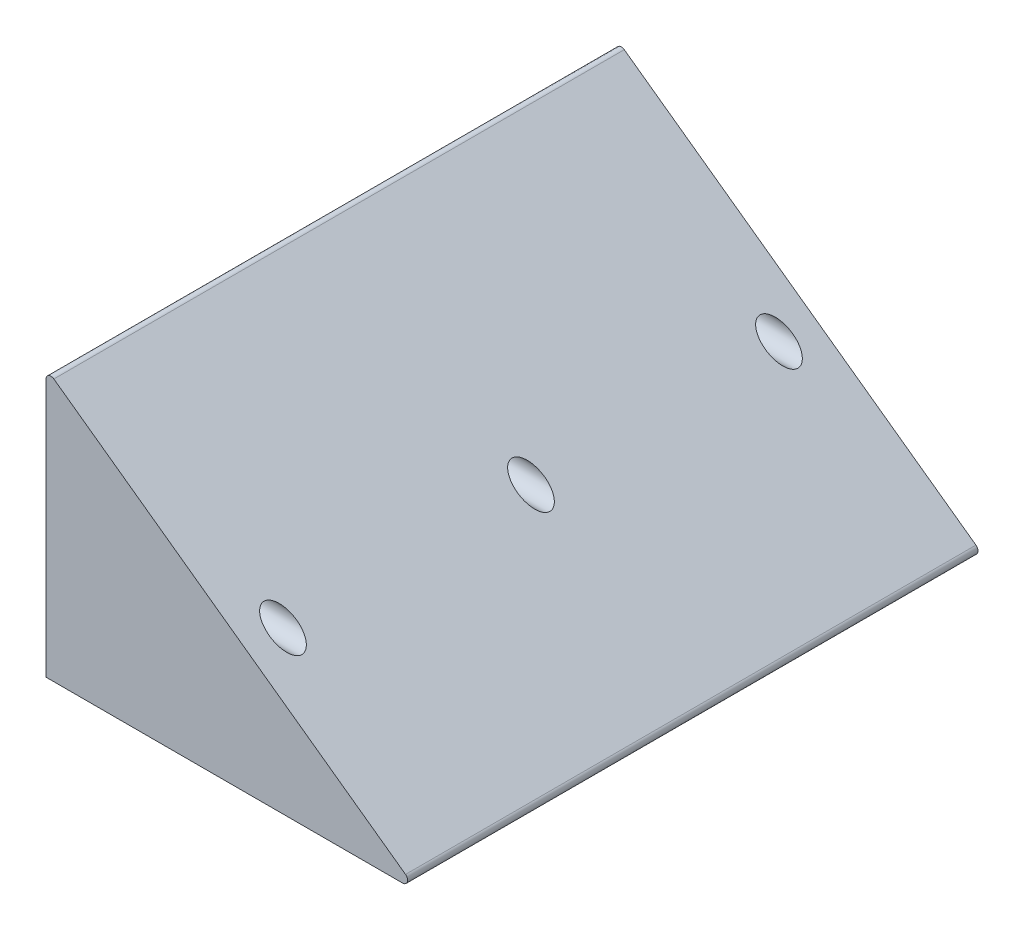
SolidWorks part; units mm, degrees
ref_plane "Ebene vorne" through (0, 0, 0) normal (0, 0, 1) x (1, 0, 0)
ref_plane "Ebene oben" through (0, 0, 0) normal (0, 1, 0) x (1, 0, 0)
ref_plane "Ebene rechts" through (0, 0, 0) normal (1, 0, 0) x (0, 0, -1)
sketch "Skizze1" plane through (0, 0, 0) normal (0, 0, 1) x (1, 0, 0)
  line L0 (0, 104.0955) -> (0, 0)
  line L1 (0, 0) -> (143.7994, 0)
  line L2 (144.968, 3.6231) -> (3.1686, 105.7186)
  arc A0 (143.7994, 0) -> (144.968, 3.6231) centre (143.7994, 2) ccw
  arc A1 (0, 104.0955) -> (3.1686, 105.7186) centre (2, 104.0955) cw
  point P6 (150, 0)
  point P9 (0, 108)
  dimension "D3" = 2
  dimension "D1" = 108
  dimension "D2" = 150
extrude "Aufsatz-Linear austragen1" add sketch "Skizze1" against normal blind 230
ref_plane "Ebene1" through (150, 0, 0) normal (1, 0, 0) x (0, 0, -1)
hole_wizard "Stirnsenkung für M6 Zylinderschraube mit Innensechskant1" positions "Skizze2" profile "Skizze4" counterbore size "M6" standard "DIN" end condition through all
sketch "Skizze2" plane through (150, 0, 0) normal (1, 0, 0) x (0, 0, -1)
  line L0 (230, 0) -> (0, 0) construction
  line L2 (230, 3.6231) -> (230, 105.7186) construction
  point P0 (15, 50)
  point P2 (115, 50)
  point P4 (215, 50)
  dimension "D1" = 50
  dimension "D2" = 15
  dimension "D3" = 115
  dimension "D4" = 215
sketch "Skizze4" plane through (150, 50, -15) normal (0, 1, 0) x (0, 0, -1)
  line L0 (0, 0) -> (0, 150)
  line L1 (0, 150) -> (3.3, 150)
  line L3 (3.3, 150) -> (3.3, 106.4)
  line L4 (3.3, 106.4) -> (5.5, 106.4)
  line L5 (5.5, 106.4) -> (5.5, 0)
  line L7 (5.5, 0) -> (0, 0)
  line L11 (0, -6.35) -> (0, 107.95) construction
  dimension "Bohrerdurchmesser" = 6.6
  dimension "Bohrungstiefe" = 150
  dimension "Senkdurchmesser2" = 11
  dimension "Senktiefe2" = 106.4
